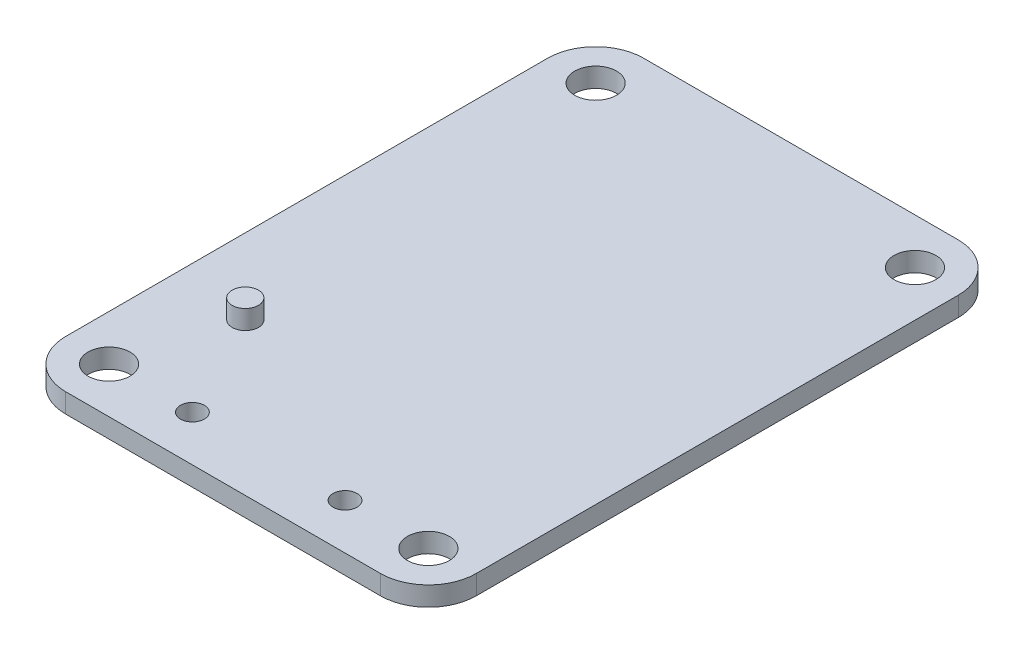
SolidWorks part; units mm, degrees
ref_plane "Front Plane" through (0, 0, 0) normal (0, 0, 1) x (1, 0, 0)
ref_plane "Top Plane" through (0, 0, 0) normal (0, 1, 0) x (1, 0, 0)
ref_plane "Right Plane" through (0, 0, 0) normal (1, 0, 0) x (0, 0, -1)
sketch "Sketch1" plane through (0, 0, 0) normal (0, 1, 0) x (1, 0, 0)
  line L0 (0, 44.26) -> (0, 4)
  line L1 (4, 0) -> (30.29, 0)
  line L2 (34.29, 4) -> (34.29, 44.26)
  line L3 (30.29, 48.26) -> (4, 48.26)
  arc A0 (0, 4) -> (4, 0) centre (4, 4) ccw
  arc A1 (30.29, 0) -> (34.29, 4) centre (30.29, 4) ccw
  arc A2 (34.29, 44.26) -> (30.29, 48.26) centre (30.29, 44.26) ccw
  arc A3 (4, 48.26) -> (0, 44.26) centre (4, 44.26) ccw
  circle A4 centre (3.81, 3.81) radius 1.75
  circle A5 centre (30.48, 3.81) radius 1.75
  circle A6 centre (3.81, 44.45) radius 1.75
  circle A7 centre (30.48, 44.45) radius 1.75
  dimension "D3" = 3.5
  dimension "D1" = 48.26
  dimension "D2" = 34.29
extrude "Boss-Extrude1" add sketch "Sketch1" along normal blind 1.62 contours L3 A3 L0 A0 L1 A1 L2 A2 A7 A6 A5 A4
sketch "Sketch2" plane through (0, 1.62, 0) normal (0, 1, 0) x (1, 0, 0)
  line L0 (17.145, 0) -> (17.145, 48.26) construction
  line L1 (4, 0) -> (30.29, 0) construction
  line L2 (30.29, 48.26) -> (4, 48.26) construction
  line L3 (17.145, 3.81) -> (10.77, 3.81) construction
  circle A0 centre (10.77, 3.81) radius 1
  circle A1 centre (23.52, 3.81) radius 1
  dimension "D3" = 2
  dimension "D1" = 3.81
  dimension "D2" = 12.75
extrude "Cut-Extrude1" cut sketch "Sketch2" against normal blind 1.62 contours A1 | A0
sketch "Sketch3" plane through (0, 1.62, 0) normal (0, 1, 0) x (1, 0, 0)
  line L0 (0, 24.13) -> (0, -10.893) construction
  line L1 (0, 44.26) -> (0, 4) construction
  line L2 (17.145, 0) -> (-10.0548, 0) construction
  line L3 (4, 0) -> (30.29, 0) construction
  circle A0 centre (6.3, 12.7) radius 1.1
  dimension "D1" = 2.2
  dimension "D2" = 6.3
  dimension "D3" = 12.7
extrude "Boss-Extrude2" add sketch "Sketch3" along normal blind 1.6 contours A0
